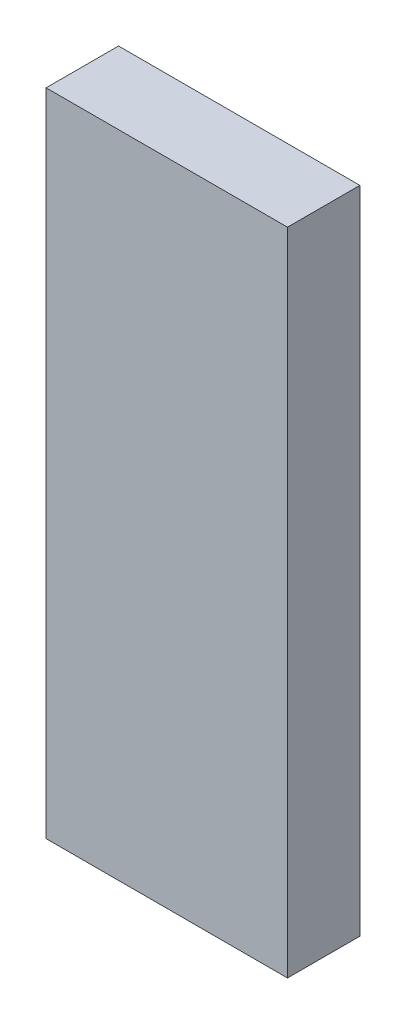
SolidWorks part; units mm, degrees
ref_plane "Plan de face" through (0, 0, 0) normal (0, 0, 1) x (1, 0, 0)
ref_plane "Plan de dessus" through (0, 0, 0) normal (0, 1, 0) x (1, 0, 0)
ref_plane "Plan de droite" through (0, 0, 0) normal (1, 0, 0) x (0, 0, -1)
sketch "Esquisse1" plane through (0, 0, 0) normal (0, 0, 1) x (1, 0, 0)
  line L1 (-91.9526, 60.2766) -> (-81.9526, 60.2766)
  line L2 (-91.9526, 60.2766) -> (-91.9526, 33.3366)
  line L3 (-91.9526, 33.3366) -> (-81.9526, 33.3366)
  line L4 (-81.9526, 60.2766) -> (-81.9526, 33.3366)
  dimension "D1" = 10
  dimension "D2" = 26.94
extrude "Boss.-Extru.1" add sketch "Esquisse1" along normal blind 3
